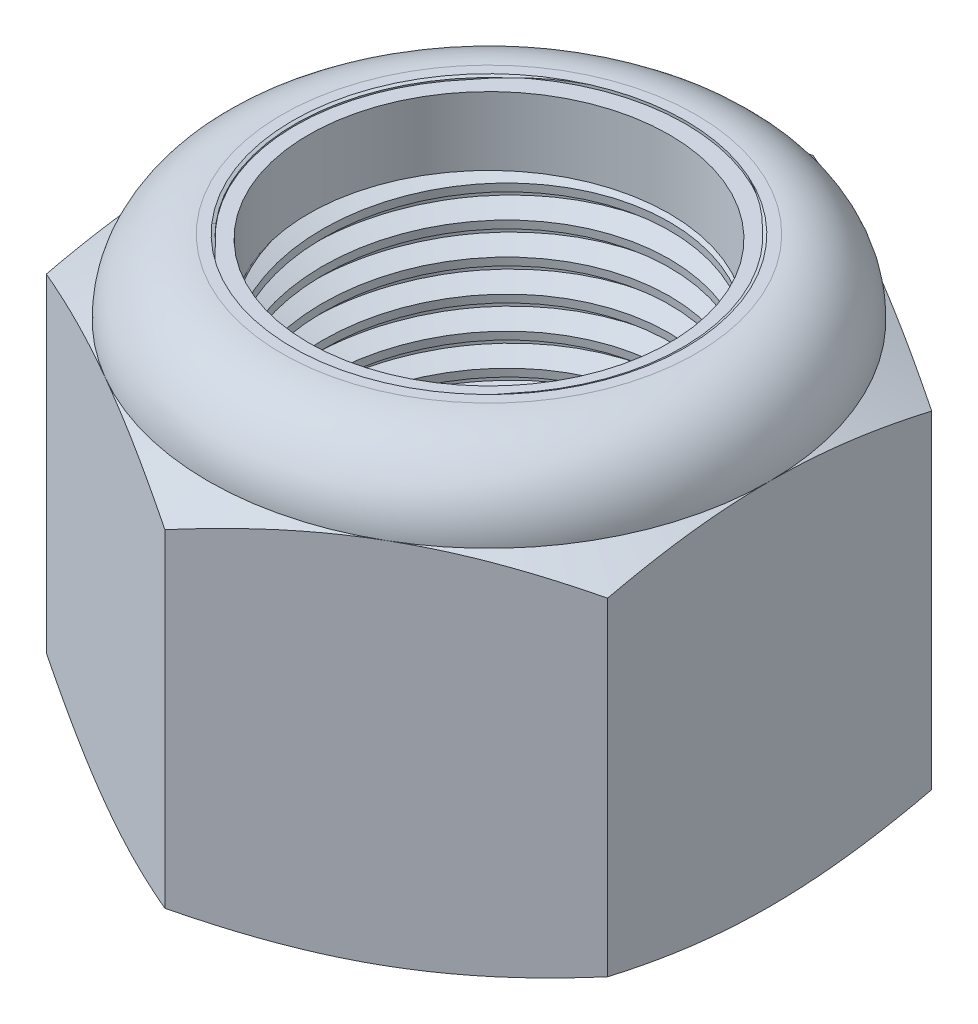
SolidWorks part; units mm, degrees
ref_plane "Front" through (0, 0, 0) normal (0, 0, 1) x (1, 0, 0)
ref_plane "Top" through (0, 0, 0) normal (0, 1, 0) x (1, 0, 0)
ref_plane "Right" through (0, 0, 0) normal (1, 0, 0) x (0, 0, -1)
sketch "Sketch1" plane through (0, 0, 0) normal (0, 1, 0) x (1, 0, 0)
  line L1 (0, 18.3309) -> (-15.875, 9.1654)
  line L2 (-15.875, 9.1654) -> (-15.875, -9.1654)
  line L3 (-15.875, -9.1654) -> (0, -18.3309)
  line L4 (0, -18.3309) -> (15.875, -9.1654)
  line L5 (15.875, -9.1654) -> (15.875, 9.1654)
  line L6 (15.875, 9.1654) -> (0, 18.3309)
  circle A0 centre (0, 0) radius 15.875 construction
  dimension "Hex Flats" = 31.75
extrude "Extrude1" add sketch "Sketch1" along normal blind 25.0031
sketch "Sketch2" plane through (0, 0, 0) normal (1, 0, 0) x (0, 0, -1)
  line L0 (-11.1125, 0) -> (-11.1125, 25.0031) construction
  line L1 (0, 0) -> (11.1125, 0)
  line L2 (0, 0) -> (0, 25.0031)
  line L3 (0, 25.0031) -> (11.1125, 25.0031)
  line L4 (11.1125, 0) -> (11.1125, 25.0031)
  line L5 (-9.1654, 25.0031) -> (9.1654, 25.0031) construction
  line L7 (0, -11.1125) -> (0, 0) construction
  dimension "Thread Dia" = 22.225
revolve "Revolve1" add sketch "Sketch2" angle 360 about L7
sketch "Sketch3" plane through (0, 0, 0) normal (1, 0, 0) x (0, 0, -1)
  line L0 (11.1125, 25.0031) -> (-11.1125, 25.0031) construction
  line L1 (-11.1125, 25.0031) -> (-11.1125, 23.1888) construction
  line L2 (-11.1125, 23.1888) -> (11.1125, 25.0031) construction
  line L3 (11.1125, 25.0031) -> (11.131, 24.7771) construction
  line L4 (11.131, 24.7771) -> (11.2601, 23.1949)
  line L5 (11.2601, 23.1949) -> (10.2352, 23.68)
  line L6 (10.2352, 23.68) -> (10.1983, 24.1321)
  line L7 (10.1983, 24.1321) -> (11.131, 24.7771)
  line L8 (10.2168, 23.9061) -> (11.1955, 23.986) construction
  line L9 (11.1125, 25.0031) -> (11.1125, 23.9792) construction
  line L10 (11.1125, 23.9792) -> (-11.1125, 22.1649) construction
  line L11 (-11.1125, 22.1649) -> (-11.1125, 23.1888) construction
  line L12 (-0.1576, 25.0031) -> (0.1576, 21.141) construction
  line L13 (-11.1125, 0) -> (-11.1125, 25.0031) construction
  line L14 (0, 25.0031) -> (11.1125, 25.0031) construction
  line L15 (11.1125, 0) -> (11.1125, 25.0031) construction
  point P13 (0, 23.0721)
  dimension "D1" = 0.2268
  dimension "D2" = 0.4536
  dimension "Thread Pitch" = 1.8143
  dimension "D4" = 60
  dimension "D5" = 1.8143
revolve "Cut-Revolve1" cut sketch "Sketch3" angle 360 about L12
pattern_linear "LPattern1" count 14 spacing 1.8143 along (0, -1, 0) count 2 spacing 1.8143 along (0, 1, 0) of "Cut-Revolve1"
sketch "Sketch4" plane through (0, 0, 0) normal (1, 0, 0) x (0, 0, -1)
  line L0 (0, 25.0031) -> (11.1125, 25.0031)
  line L1 (11.1125, 25.0031) -> (10.1983, 24.5768)
  line L2 (10.1983, 24.5768) -> (10.1983, 0.4263)
  line L3 (10.1983, 0.4263) -> (11.1125, 0)
  line L4 (11.1125, 0) -> (0, 0)
  line L5 (0, 0) -> (0, 25.0031)
  line L6 (11.1125, 0) -> (11.1125, 25.0031) construction
  line L7 (0, 25.0031) -> (11.1125, 25.0031) construction
  line L8 (0, 0) -> (11.1125, 0) construction
  line L9 (0, 0) -> (0, 25.0031) construction
  line L10 (0, 25.0031) -> (0, 26.0118) construction
  dimension "D1" = 25
revolve "Cut-Revolve2" cut sketch "Sketch4" angle 360 about L10
combine bodies "Combine1" operation type subtract main body 112 bodies to subtract 111
sketch "Sketch5" plane through (0, 0, 0) normal (1, 0, 0) x (0, 0, -1)
  line L0 (0, 0) -> (15.875, 0)
  line L1 (15.875, 0) -> (18.3309, 1.1452)
  line L2 (18.3309, 1.1452) -> (18.3309, 19.6907)
  line L3 (18.3309, 19.6907) -> (15.875, 20.8359)
  line L4 (11.7078, 25.0031) -> (11.7078, 26.2731)
  line L5 (11.7078, 26.2731) -> (19.6009, 26.2731)
  line L6 (19.6009, 26.2731) -> (19.6009, -1.27)
  line L7 (19.6009, -1.27) -> (0, -1.27)
  line L8 (0, -1.27) -> (0, 0)
  line L9 (15.875, 20.8359) -> (15.875, 0) construction
  line L10 (0, 0) -> (11.1125, 0) construction
  line L13 (18.3309, 10.418) -> (19.6009, 10.418) construction
  line L14 (18.3309, 25.0031) -> (18.3309, 0) construction
  line L15 (0, 0) -> (0, 26.2731) construction
  line L20 (0, 26.2731) -> (11.7078, 26.2731) construction
  line L22 (0, 25.0031) -> (11.1125, 25.0031) construction
  arc A0 (15.875, 20.8359) -> (11.7078, 25.0031) centre (11.7078, 20.8359) ccw
  dimension "D1" = 25
  dimension "D2" = 1.27
  dimension "D3" = 25.0031
  dimension "D4" = 4.1672
revolve "Cut-Revolve3" cut sketch "Sketch5" angle 360 about L15
sketch "Sketch6" plane through (0, 0, 0) normal (1, 0, 0) x (0, 0, -1)
  line L0 (0, 20.8359) -> (15.7226, 20.8359)
  line L1 (11.7078, 24.8507) -> (10.9531, 24.8507)
  line L2 (0, 26.2731) -> (0, 20.8359)
  line L3 (10.9531, 26.2731) -> (0, 26.2731)
  line L4 (0, 26.2731) -> (11.7078, 26.2731) construction
  line L5 (0, 0) -> (0, 26.2731) construction
  line L6 (0, 26.2731) -> (0, 44.323) construction
  line L7 (10.9531, 24.8507) -> (10.9531, 26.2731)
  line L8 (11.7078, 25.0031) -> (11.7078, 24.8507) construction
  line L9 (10.9531, 24.8507) -> (10.1983, 24.8507) construction
  line L10 (10.1983, 24.8507) -> (10.1983, 24.5768) construction
  arc A0 (15.7226, 20.8359) -> (11.7078, 24.8507) centre (11.7078, 20.8359) ccw
  arc A1 (15.875, 20.8359) -> (11.7078, 25.0031) centre (11.7078, 20.8359) ccw construction
  dimension "D1" = 0.1524
revolve "Cut-Revolve4" cut sketch "Sketch6" angle 360 about L6
sketch "Sketch7" plane through (0, 0, 0) normal (1, 0, 0) x (0, 0, -1)
  line L0 (10.1983, 20.9121) -> (15.6457, 20.9121)
  line L1 (11.7078, 24.7745) -> (10.1983, 24.7745)
  line L2 (10.1983, 24.7745) -> (10.1983, 20.9121)
  line L3 (10.1983, 20.9121) -> (0, 20.9121) construction
  line L4 (0, 20.9121) -> (0, 24.7745) construction
  line L5 (0, 24.7745) -> (10.1983, 24.7745) construction
  line L6 (10.1983, 20.9121) -> (10.1983, 20.8359) construction
  line L7 (0, 20.8359) -> (15.7226, 20.8359) construction
  line L8 (11.7078, 24.7745) -> (11.7078, 24.8507) construction
  arc A0 (15.6457, 20.9121) -> (11.7078, 24.7745) centre (11.7078, 20.8359) ccw
  arc A2 (15.7226, 20.8359) -> (11.7078, 24.8507) centre (11.7078, 20.8359) ccw construction
  dimension "D1" = 0.0762
revolve "Revolve2" add sketch "Sketch7" angle 360 about L4
equation "\"D1@Sketch3\"=\"Thread Pitch@Sketch3\"/8"
equation "\"D2@Sketch3\"=\"Thread Pitch@Sketch3\"/4"
equation "\"D5@Sketch3\"=\"Thread Pitch@Sketch3\""
equation "\"D4@LPattern1\"=\"Thread Pitch@Sketch3\""
equation "\"D3@LPattern1\"=\"Thread Pitch@Sketch3\""
equation "\"D1@LPattern1\"=\"Height@Extrude1\"/\"Thread Pitch@Sketch3\""
equation "\"D4@Sketch5\"=\"Height@Extrude1\"/6"
